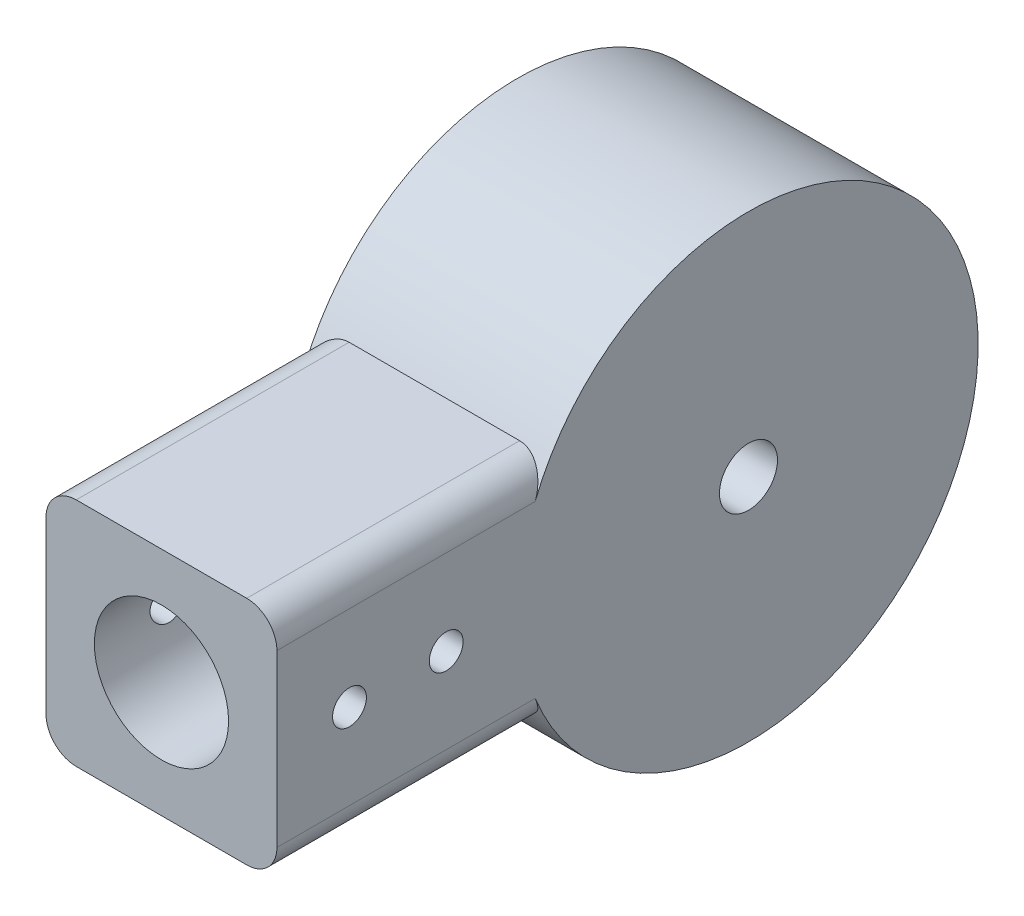
SolidWorks part; units mm, degrees
ref_plane "Front Plane" through (0, 0, 0) normal (0, 0, 1) x (1, 0, 0)
ref_plane "Top Plane" through (0, 0, 0) normal (0, 1, 0) x (1, 0, 0)
ref_plane "Right Plane" through (0, 0, 0) normal (1, 0, 0) x (0, 0, -1)
sketch "Sketch1" plane through (0, 0, 0) normal (0, 1, 0) x (1, 0, 0)
  line L0 (-5.55, -20) -> (-9.55, -20)
  line L1 (-5.55, -20) -> (5.55, -20)
  line L2 (-5.55, -20) -> (-5.55, 0)
  line L3 (-5.55, 0) -> (5.55, 0)
  line L4 (5.55, -20) -> (5.55, 0)
  line L5 (-5.55, -20) -> (5.55, 0) construction
  line L6 (-5.55, 0) -> (5.55, -20) construction
  line L7 (-9.55, -20) -> (-9.55, 0)
  line L8 (-9.55, 4) -> (5.95, 4)
  line L9 (5.95, 4) -> (5.95, 10.55)
  line L10 (5.95, 10.55) -> (-6.05, 10.55)
  line L11 (-6.05, 10.55) -> (-6.05, 27.45)
  line L12 (-6.05, 27.45) -> (5.95, 27.45)
  line L13 (5.95, 27.45) -> (5.95, 34)
  line L14 (5.95, 34) -> (-9.55, 34)
  line L15 (-9.55, 34) -> (-9.55, 38)
  line L16 (-9.55, 38) -> (9.55, 38)
  line L17 (-6.05, 19) -> (-24.2593, 19) construction
  line L18 (9.55, -20) -> (5.55, -20)
  line L19 (-9.55, 0) -> (-9.55, 4)
  line L20 (9.55, 38) -> (9.55, 0)
  line L21 (0, -10) -> (0, 0) construction
  line L22 (9.55, 0) -> (9.55, -20)
  line L23 (-6.05, 19) -> (1.75, 19) construction
  line L24 (-6.05, 21.4) -> (9.55, 21.4)
  line L25 (-6.05, 21.4) -> (-6.05, 16.6)
  line L26 (-6.05, 16.6) -> (9.55, 16.6)
  line L27 (9.55, 21.4) -> (9.55, 16.6)
  line L28 (-6.05, 21.4) -> (9.55, 16.6) construction
  line L29 (-6.05, 16.6) -> (9.55, 21.4) construction
  line L30 (-9.55, 0) -> (-5.55, 0) construction
  line L31 (5.55, 0) -> (9.55, 0) construction
  point P0 (0, -10)
  point P25 (1.75, 19)
  dimension "D1" = 11.1
  dimension "D2" = 4
  dimension "D3" = 20
  dimension "D4" = 30
  dimension "D5" = 16.9
  dimension "D6" = 4.8
  dimension "D7" = 12
  dimension "D8" = 4
  dimension "D9" = 3.5
sketch "Sketch2" plane through (0, 0, 0) normal (0, 1, 0) x (1, 0, 0)
  line L1 (-6.05, 21.4) -> (9.55, 21.4) construction
  line L2 (-6.05, 16.6) -> (9.55, 16.6) construction
  line L3 (9.55, 38) -> (9.55, 0) construction
  line L4 (-9.55, 38) -> (9.55, 38) construction
  line L5 (-9.55, 34) -> (-9.55, 38) construction
  line L6 (5.95, 34) -> (-9.55, 34) construction
  line L7 (5.95, 27.45) -> (5.95, 34) construction
  line L8 (-6.05, 27.45) -> (5.95, 27.45) construction
  line L9 (-6.05, 10.55) -> (-6.05, 27.45) construction
  line L10 (5.95, 10.55) -> (-6.05, 10.55) construction
  line L11 (5.95, 4) -> (5.95, 10.55) construction
  line L12 (-9.55, 4) -> (5.95, 4) construction
  line L13 (-9.55, 0) -> (-9.55, 4) construction
  line L14 (5.55, 0) -> (9.55, 0) construction
  line L15 (-5.55, 0) -> (5.55, 0) construction
  line L16 (-9.55, 0) -> (-5.55, 0) construction
  line L17 (-6.05, 19) -> (-24.2593, 19) construction
  line L18 (-6.05, 21.4) -> (9.55, 21.4)
  line L19 (-6.05, 16.6) -> (9.55, 16.6)
  line L20 (9.55, 38) -> (9.55, 21.4)
  line L21 (-9.55, 38) -> (9.55, 38)
  line L22 (-9.55, 34) -> (-9.55, 38)
  line L23 (5.95, 34) -> (-9.55, 34)
  line L24 (5.95, 27.45) -> (5.95, 34)
  line L25 (-6.05, 27.45) -> (5.95, 27.45)
  line L26 (-6.05, 10.55) -> (-6.05, 16.6)
  line L27 (5.95, 10.55) -> (-6.05, 10.55)
  line L28 (5.95, 4) -> (5.95, 10.55)
  line L29 (-9.55, 4) -> (5.95, 4)
  line L30 (-9.55, 0) -> (-9.55, 4)
  line L31 (5.55, 0) -> (9.55, 0)
  line L32 (-5.55, 0) -> (5.55, 0)
  line L33 (-9.55, 0) -> (-5.55, 0)
  line L34 (-6.05, 21.4) -> (-6.05, 27.45)
  line L35 (9.55, 16.6) -> (9.55, 0)
  line L36 (-6.05, 19) -> (1.75, 19) construction
  line L37 (-6.05, 19) -> (-24.2593, 19) construction
  line L38 (-6.05, 19) -> (1.75, 19) construction
revolve "Revolve1" add sketch "Sketch2" angle 360 about L37
sketch "Sketch3" plane through (0, 0, 0) normal (0, 0, 1) x (1, 0, 0)
  line L0 (-9.55, 0) -> (9.55, 0) construction
  line L1 (-5.55, 0) -> (5.55, 0) construction
  line L2 (-5.55, 0) -> (5.55, 0)
  line L3 (-9.55, 19) -> (-9.55, -19) construction
  line L4 (9.55, 9.55) -> (-9.55, 9.55)
  line L5 (9.55, 9.55) -> (9.55, -9.55)
  line L6 (9.55, -9.55) -> (-9.55, -9.55)
  line L7 (-9.55, 9.55) -> (-9.55, -9.55)
  line L8 (9.55, 9.55) -> (-9.55, -9.55) construction
  line L9 (9.55, -9.55) -> (-9.55, 9.55) construction
  circle A0 centre (0, 0) radius 5.55
  point P4 (9.55, 0)
  point P5 (-9.55, 0)
  point P16 (0, 0)
extrude "Boss-Extrude1" add sketch "Sketch3" along normal up to vertex and the other way up to surface contours L4 L7 L6 L5 A0
fillet "Fillet1" radius 2.5 4 edges at (-9.55, 9.55, 8.7128) (-9.55, -9.55, 8.7128) (9.55, 9.55, 8.7128) (9.55, -9.55, 8.7128)
sketch "Sketch4" plane through (0, 0, 0) normal (1, 0, 0) x (0, 0, -1)
  line L0 (-6, 0) -> (0, 0) construction
  line L1 (-6, 0) -> (-14, 0) construction
  line L3 (-14, 0) -> (-20, 0) construction
  line L4 (-20, 7.05) -> (-20, -7.05) construction
  circle A0 centre (-6, 0) radius 1.4
  circle A1 centre (-14, 0) radius 1.4
  point P6 (-14.0712, 0)
  dimension "D1" = 2.8
  dimension "D2" = 8
extrude "Cut-Extrude1" cut sketch "Sketch4" against normal through all both and the other way through all
